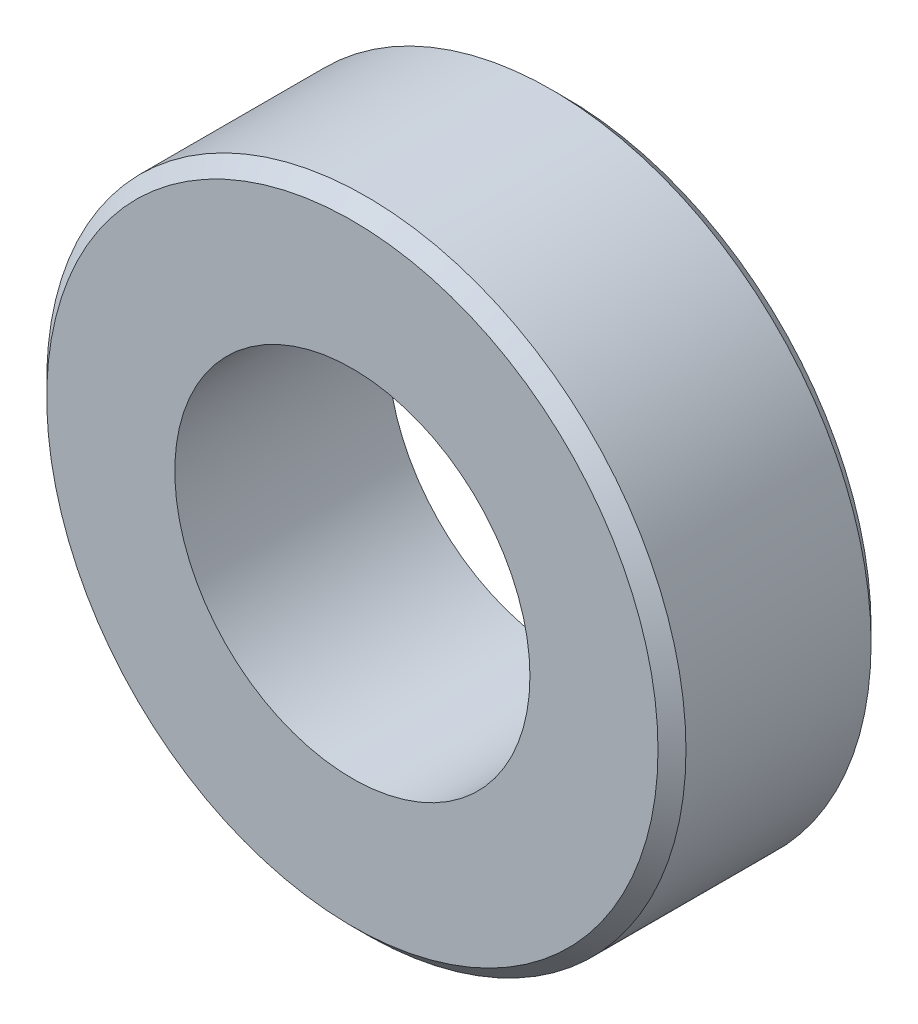
SolidWorks part; units mm, degrees
ref_plane "Front Plane" through (0, 0, 0) normal (0, 0, 1) x (1, 0, 0)
ref_plane "Top Plane" through (0, 0, 0) normal (0, 1, 0) x (1, 0, 0)
ref_plane "Right Plane" through (0, 0, 0) normal (1, 0, 0) x (0, 0, -1)
sketch "Sketch1" plane through (0, 0, 0) normal (0, 0, 1) x (1, 0, 0)
  circle A0 centre (0, 0) radius 11.43
  circle A1 centre (0, 0) radius 6.35
  dimension "D1" = 22.86
  dimension "D2" = 12.7
extrude "Boss-Extrude1" add sketch "Sketch1" along normal blind 7.62
chamfer "Chamfer1" distance 0.5 angle 45 2 edges at (11.43, 0, 0) (11.43, 0, 7.62)
